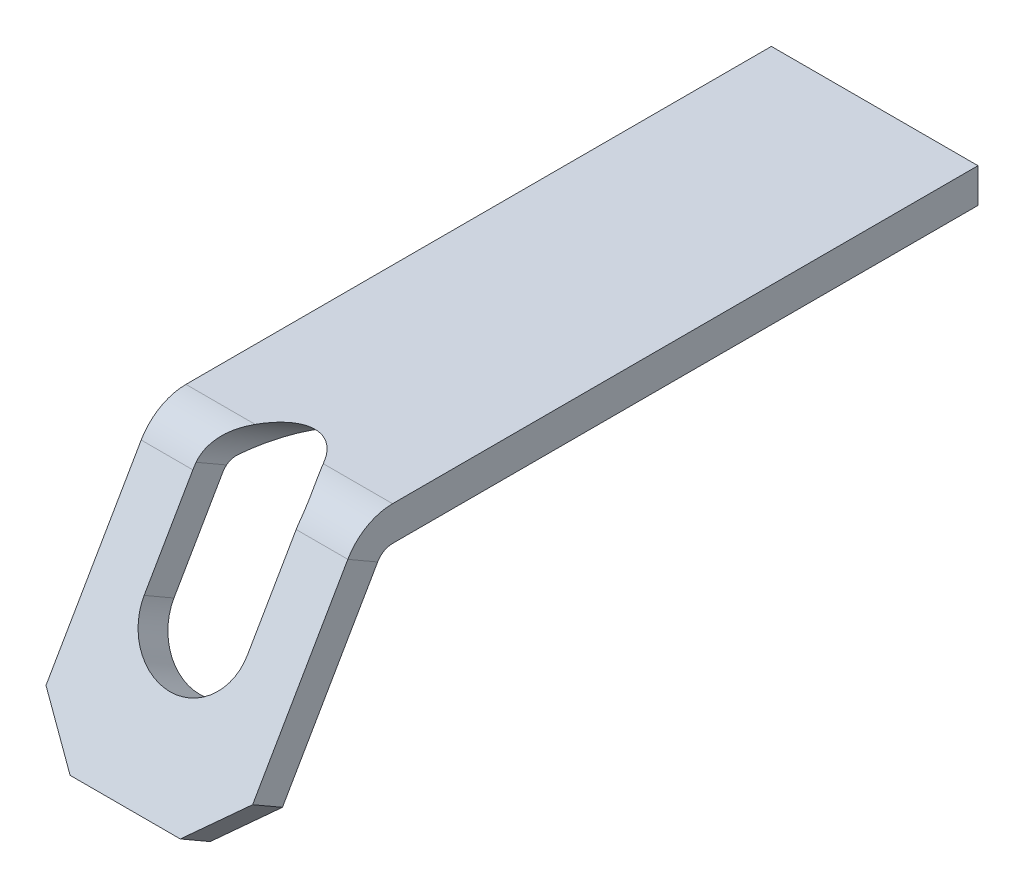
SolidWorks part; units mm, degrees
material "Brass"
ref_plane "Front Plane" through (0, 0, 0) normal (0, 0, 1) x (1, 0, 0)
ref_plane "Top Plane" through (0, 0, 0) normal (0, 1, 0) x (1, 0, 0)
ref_plane "Right Plane" through (0, 0, 0) normal (1, 0, 0) x (0, 0, -1)
sketch "Sketch1" plane through (0, 0, 0) normal (0, 1, 0) x (1, 0, 0)
  line L1 (-1.5, 4.25) -> (1.5, 4.25)
  line L2 (-1.5, 4.25) -> (-1.5, -4.25)
  line L3 (-1.5, -4.25) -> (1.5, -4.25)
  line L4 (1.5, 4.25) -> (1.5, -4.25)
  line L5 (-1.5, 4.25) -> (1.5, -4.25) construction
  line L6 (-1.5, -4.25) -> (1.5, 4.25) construction
  point P0 (0, 0)
  dimension "D1" = 8.5
  dimension "D2" = 3
extrude "Boss-Extrude1" add sketch "Sketch1" along normal mid plane 0.5
sketch "Sketch4" plane through (0, 0, 4.25) normal (0, 0, 1) x (1, 0, 0)
  line L4 (-1.5, -0.25) -> (1.5, -0.25)
  line L5 (1.5, -0.25) -> (1.5, 0.25)
  line L6 (1.5, 0.25) -> (-1.5, 0.25)
  line L7 (-1.5, 0.25) -> (-1.5, -0.25)
  line L8 (-1.5, -0.25) -> (1.5, -0.25)
  line L9 (1.5, -0.25) -> (1.5, 0.25)
  line L10 (1.5, 0.25) -> (-1.5, 0.25)
  line L11 (-1.5, 0.25) -> (-1.5, -0.25)
  dimension "D1" = 0
sketch "Sketch5" plane through (0, 0, 0) normal (1, 0, 0) x (0, 0, -1)
  line L0 (-4.683, -0.25) -> (-6.4151, -3.25)
  line L1 (-4.25, 0.25) -> (-4.25, -0.25) construction
  line L2 (-4.683, -0.25) -> (-4.25, -0.25) construction
  line L3 (-4.25, 0.25) -> (4.25, 0.25) construction
  arc A0 (-4.25, 0) -> (-4.683, -0.25) centre (-4.25, -0.5) ccw
  point P7 (-5.386, -1.2922)
  dimension "D1" = 0.5
  dimension "D2" = 0.5
  dimension "D3" = 30
  dimension "D4" = 3
  dimension "D5" = 3.5
sweep "Sweep1" add profiles "Sketch4" path "Sketch5"
sketch "Sketch6" plane through (0, 2.0903, 3.6205) normal (0, 0.5, 0.866) x (1, 0, 0)
  line L0 (0, -2.4721) -> (0, -3.9721) construction
  line L1 (0.75, -2.4721) -> (0.75, -3.9721)
  line L2 (-0.75, -2.4721) -> (-0.75, -3.9721)
  line L3 (0, -6.0221) -> (0, -4.7221) construction
  line L4 (1.5, -6.0221) -> (-1.5, -6.0221) construction
  arc A0 (0.75, -2.4721) -> (-0.75, -2.4721) centre (0, -2.4721) ccw
  arc A1 (-0.75, -3.9721) -> (0.75, -3.9721) centre (0, -3.9721) ccw
  point P3 (0, -3.2221)
  dimension "D2" = 0.75
  dimension "D1" = 1.5
  dimension "D3" = 1.3
extrude "Cut-Extrude1" cut sketch "Sketch6" against normal through all
chamfer "Chamfer1" distance 0.7 angle 45 2 edges at (1.5, -3.25, 6.4151) (-1.5, -3.25, 6.4151)
